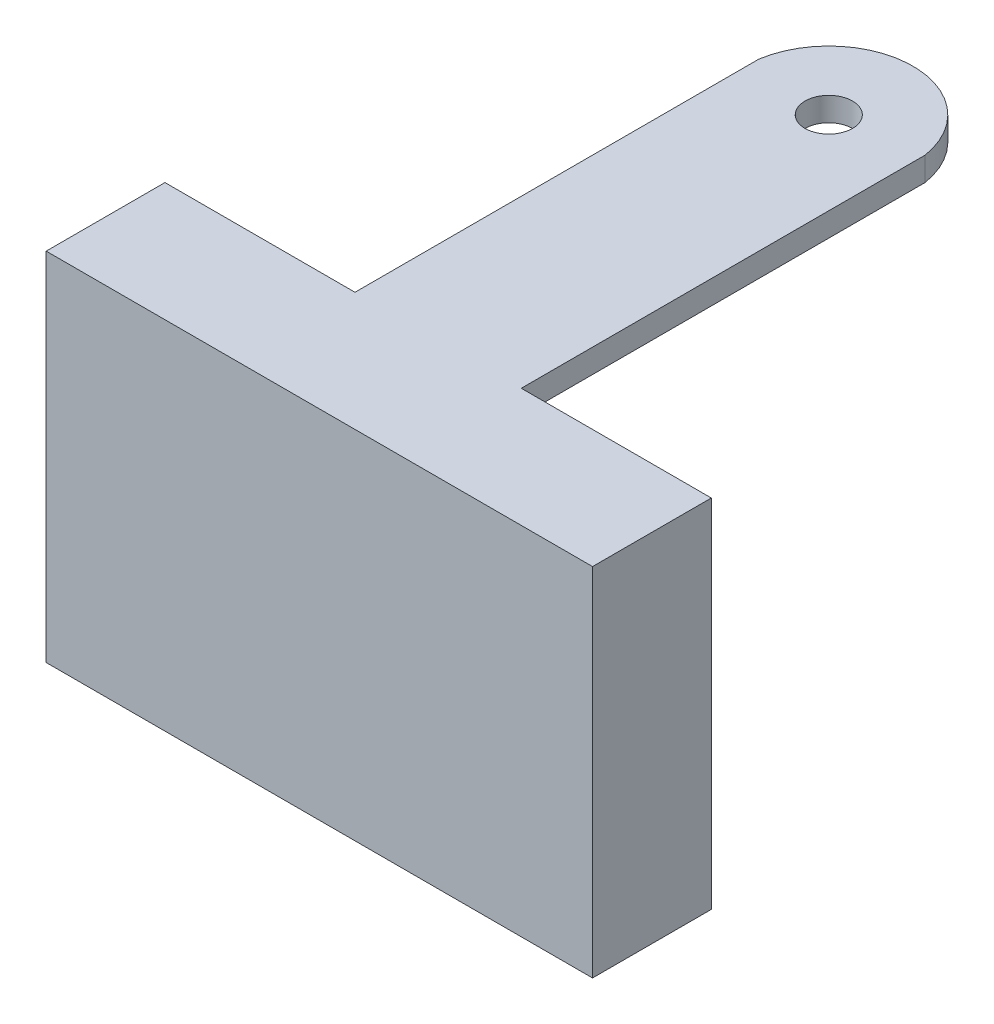
SolidWorks part; units mm, degrees
ref_plane "Front Plane" through (0, 0, 0) normal (0, 0, 1) x (1, 0, 0)
ref_plane "Top Plane" through (0, 0, 0) normal (0, 1, 0) x (1, 0, 0)
ref_plane "Right Plane" through (0, 0, 0) normal (1, 0, 0) x (0, 0, -1)
sketch "Sketch1" plane through (0, 0, 0) normal (0, 1, 0) x (1, 0, 0)
  line L1 (-11.5, 2.5) -> (11.5, 2.5)
  line L2 (-11.5, 2.5) -> (-11.5, -2.5)
  line L3 (-11.5, -2.5) -> (11.5, -2.5)
  line L4 (11.5, 2.5) -> (11.5, -2.5)
  line L5 (-11.5, 2.5) -> (11.5, -2.5) construction
  line L6 (-11.5, -2.5) -> (11.5, 2.5) construction
  point P0 (0, 0)
  dimension "D1" = 23
  dimension "D2" = 5
extrude "Boss-Extrude1" add sketch "Sketch1" along normal blind 15
sketch "Sketch3" plane through (0, 15, 0) normal (0, 1, 0) x (1, 0, 0)
  line L0 (-3.5, 2.5) -> (-3.5, 19.5)
  line L1 (11.5, 2.5) -> (-11.5, 2.5) construction
  line L2 (3.5, 2.5) -> (3.5, 19.5)
  arc A0 (-3.5, 19.5) -> (3.5, 19.5) centre (0, 18.9452) cw
  circle A1 centre (0, 18.9452) radius 1
  line M3 (11.5, 2.5) -> (-11.5, 2.5)
  dimension "D3" = 2
  dimension "D1" = 17
  dimension "D2" = 7
extrude "Boss-Extrude4" add sketch "Sketch3" against normal blind 1 contours A0 L0 L2 A1 M3
